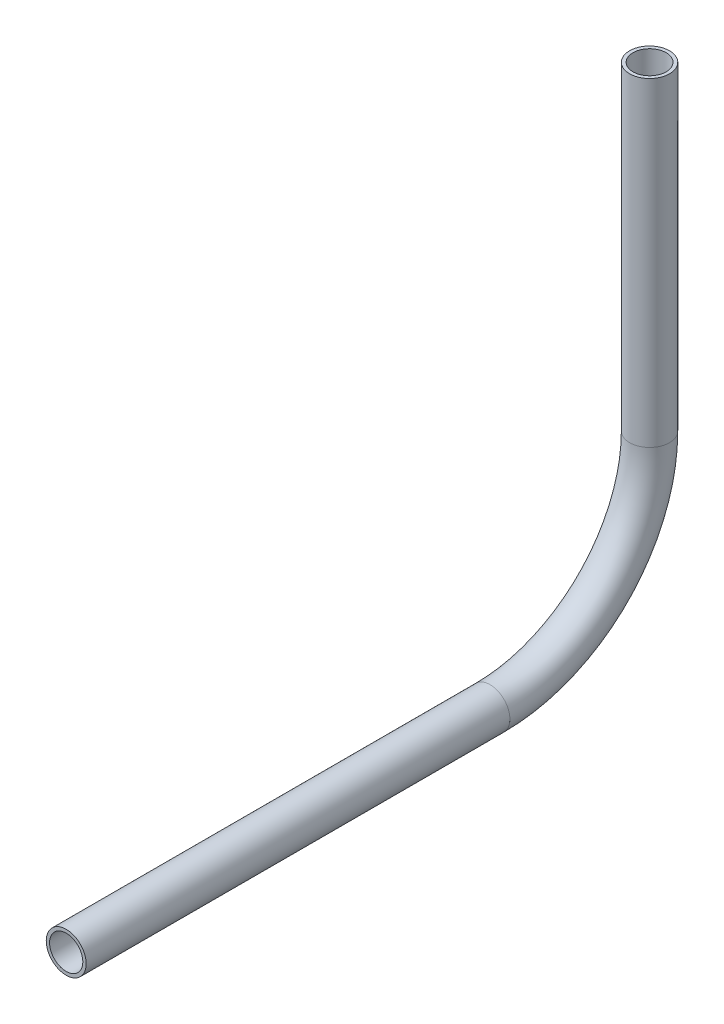
SolidWorks part; units mm, degrees
ref_plane "Front Plane" through (0, 0, 0) normal (0, 0, 1) x (1, 0, 0)
ref_plane "Top Plane" through (0, 0, 0) normal (0, 1, 0) x (1, 0, 0)
ref_plane "Right Plane" through (0, 0, 0) normal (1, 0, 0) x (0, 0, -1)
sketch "Sketch1" plane through (0, 0, 0) normal (1, 0, 0) x (0, 0, -1)
  line L0 (-303.1646, 599.96) -> (-168.2735, 599.96)
  line L1 (-117.4735, 650.76) -> (-117.4735, 752.4586)
  arc A0 (-168.2735, 599.96) -> (-117.4735, 650.76) centre (-168.2735, 650.76) ccw
  dimension "D1" = 50.8
other "Pipe 0.5 SCH 40(1)"
ref_plane "Plane1" through (0, 599.96, 303.1646) normal (0, 0, -1) x (0, 1, 0)
sketch "Sketch11" plane through (0, 599.96, 303.1646) normal (0, 0, -1) x (0, 1, 0)
  circle A0 centre (0, 0) radius 5.2832
  circle A1 centre (0, 0) radius 6.35
  point P5 (0, 0)
  dimension "In_dia" = 10.5664
  dimension "Out_dia" = 12.7
